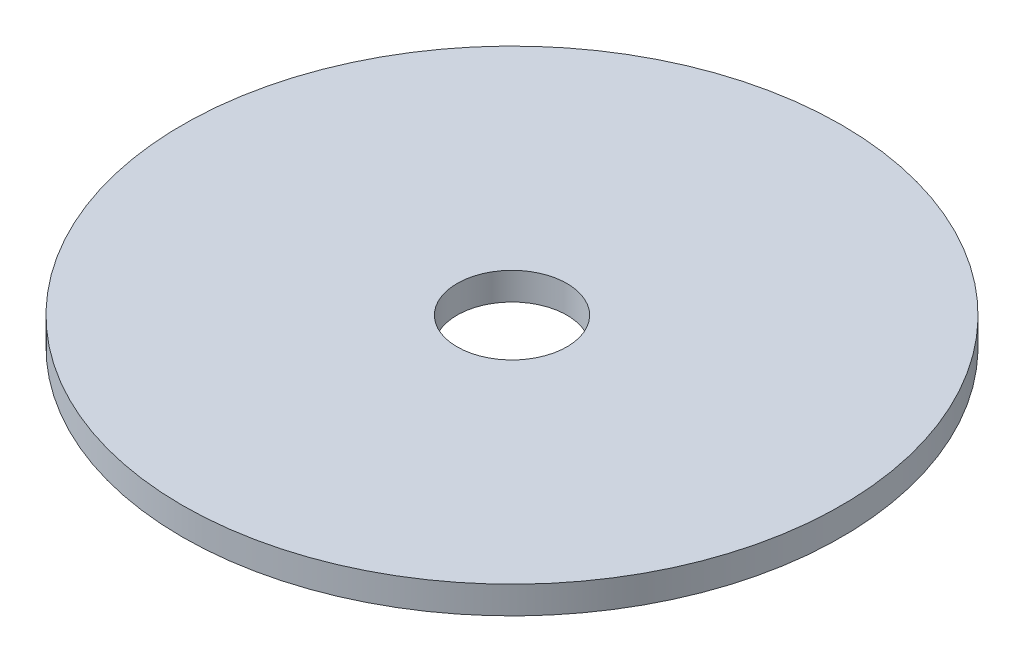
SolidWorks part; units mm, degrees
ref_plane "Front Plane" through (0, 0, 0) normal (0, 0, 1) x (1, 0, 0)
ref_plane "Top Plane" through (0, 0, 0) normal (0, 1, 0) x (1, 0, 0)
ref_plane "Right Plane" through (0, 0, 0) normal (1, 0, 0) x (0, 0, -1)
sketch "Sketch1" plane through (0, 0, 0) normal (0, 1, 0) x (1, 0, 0)
  circle A0 centre (0, 0) radius 30
  dimension "D1" = 60
extrude "Boss-Extrude2" add sketch "Sketch1" along normal blind 2.5
sketch "Sketch2" plane through (0, 2.5, 0) normal (0, 1, 0) x (1, 0, 0)
  circle A0 centre (0, 0) radius 5
  dimension "D1" = 10
extrude "Cut-Extrude2" cut sketch "Sketch2" against normal blind 2.5
